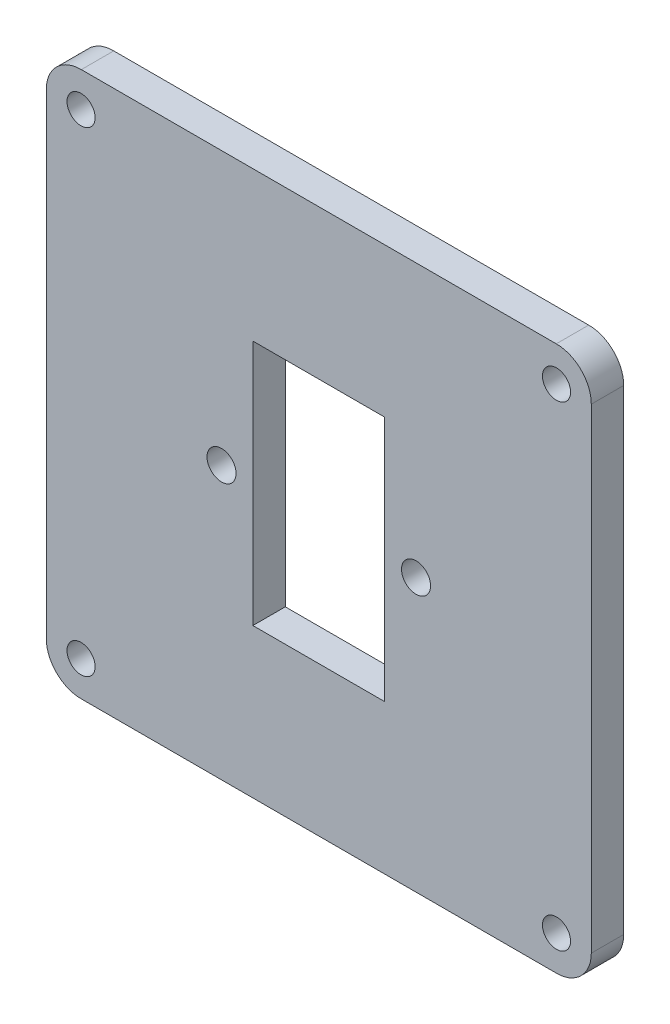
SolidWorks part; units mm, degrees
ref_plane "Front Plane" through (0, 0, 0) normal (0, 0, 1) x (1, 0, 0)
ref_plane "Top Plane" through (0, 0, 0) normal (0, 1, 0) x (1, 0, 0)
ref_plane "Right Plane" through (0, 0, 0) normal (1, 0, 0) x (0, 0, -1)
sketch "Model" plane through (0, 0, 0) normal (0, 0, 1) x (1, 0, 0)
  line L1 (25.6398, 69.0896) -> (69.5928, 69.0896)
  line L2 (47.6163, 69.0896) -> (47.6163, 18.654) construction
  line L3 (41.5163, 55.2721) -> (53.7163, 55.2721)
  line L4 (41.5163, 32.4721) -> (41.5163, 55.2721)
  line L5 (53.7163, 32.4721) -> (41.5163, 32.4721)
  line L6 (53.7163, 55.2721) -> (53.7163, 32.4721)
  line L7 (69.591, 18.654) -> (25.6416, 18.654)
  line L9 (22.3984, 21.8721) -> (22.3984, 65.8721)
  line L10 (72.8342, 21.8721) -> (72.8342, 65.8722)
  line L11 (22.3984, 43.8721) -> (72.8342, 43.8721) construction
  line L12 (25.6163, 21.8718) -> (69.6163, 21.8718) construction
  line L13 (25.6163, 65.8718) -> (25.6163, 21.8718) construction
  line L14 (25.6163, 65.8718) -> (69.6163, 65.8718) construction
  line L15 (69.6163, 65.8718) -> (69.6163, 21.8718) construction
  circle A0 centre (25.6163, 65.8718) radius 1.3
  circle A1 centre (69.6163, 65.8718) radius 1.3
  circle A2 centre (56.6163, 43.8721) radius 1.3441
  circle A3 centre (38.6163, 43.8721) radius 1.3441
  circle A4 centre (25.6163, 21.8718) radius 1.3
  circle A5 centre (69.6163, 21.8718) radius 1.3
  arc A6 (72.8342, 65.8722) -> (69.5928, 69.0896) centre (69.6163, 65.8718) ccw
  arc A7 (22.3984, 21.8721) -> (25.6416, 18.654) centre (25.6163, 21.8718) ccw
  arc A8 (69.591, 18.654) -> (72.8342, 21.8721) centre (69.6163, 21.8718) ccw
  arc A9 (25.6398, 69.0896) -> (22.3984, 65.8721) centre (25.6163, 65.8718) ccw
  dimension "D1" = 12.2
  dimension "D2" = 18
  dimension "D4" = 44
  dimension "D5" = 44
  dimension "D3" = 22.8
extrude "Boss-Extrude1" add sketch "Model" along normal blind 3
